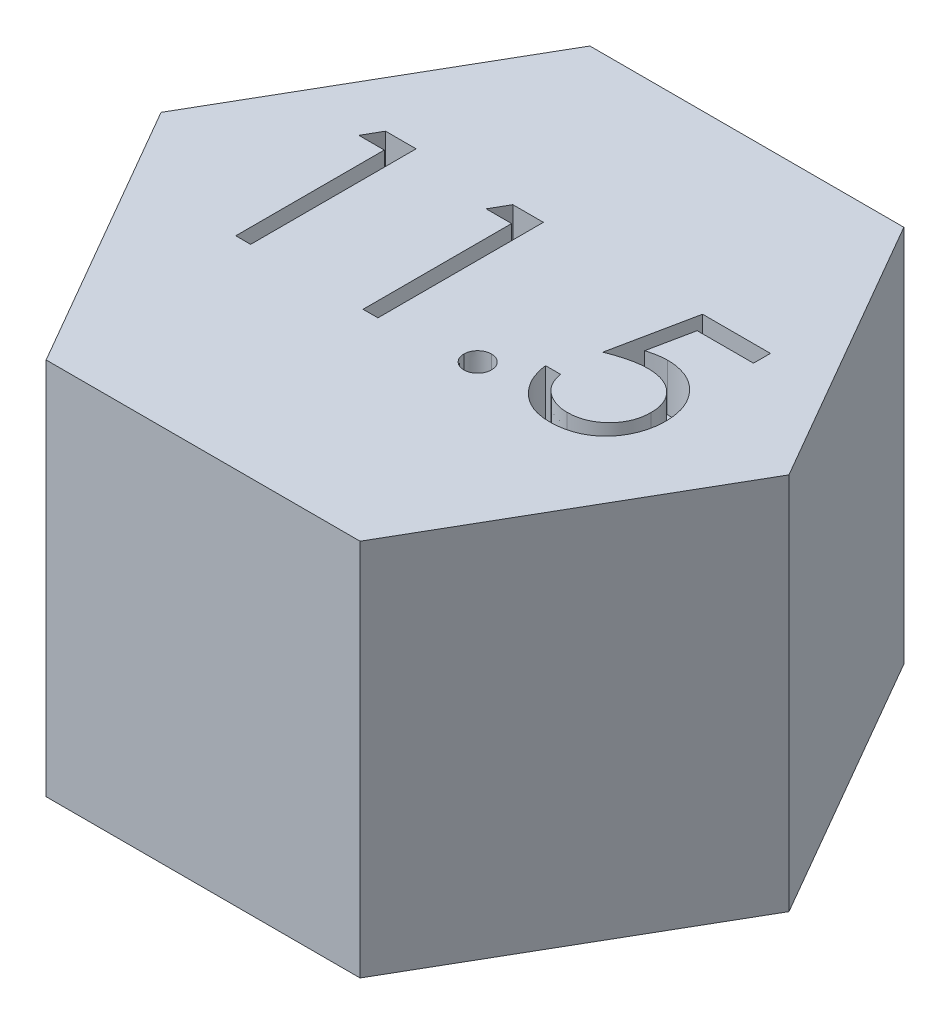
SolidWorks part; units mm, degrees
ref_plane "Front Plane" through (0, 0, 0) normal (0, 0, 1) x (1, 0, 0)
ref_plane "Top Plane" through (0, 0, 0) normal (0, 1, 0) x (1, 0, 0)
ref_plane "Right Plane" through (0, 0, 0) normal (1, 0, 0) x (0, 0, -1)
sketch "Sketch2" plane through (0, 0, 0) normal (0, 1, 0) x (1, 0, 0)
  line L1 (3.3198, 5.75) -> (-3.3198, 5.75)
  line L2 (-3.3198, 5.75) -> (-6.6395, 0)
  line L3 (-6.6395, 0) -> (-3.3198, -5.75)
  line L4 (-3.3198, -5.75) -> (3.3198, -5.75)
  line L5 (3.3198, -5.75) -> (6.6395, 0)
  line L6 (6.6395, 0) -> (3.3198, 5.75)
  circle A0 centre (0, 0) radius 5.75 construction
  circle A1 centre (0, 0) radius 5.75 construction
  dimension "D1" = 11.5
extrude "Boss-Extrude1" add sketch "Sketch2" along normal blind 8 contours L2 L3 L4 L5 L6 L1
sketch "Sketch7" plane through (0, 8, 0) normal (0, 1, 0) x (1, 0, 0)
  text T0 "11.5"
extrude "Cut-Extrude1" cut sketch "Sketch7" against normal blind 1
